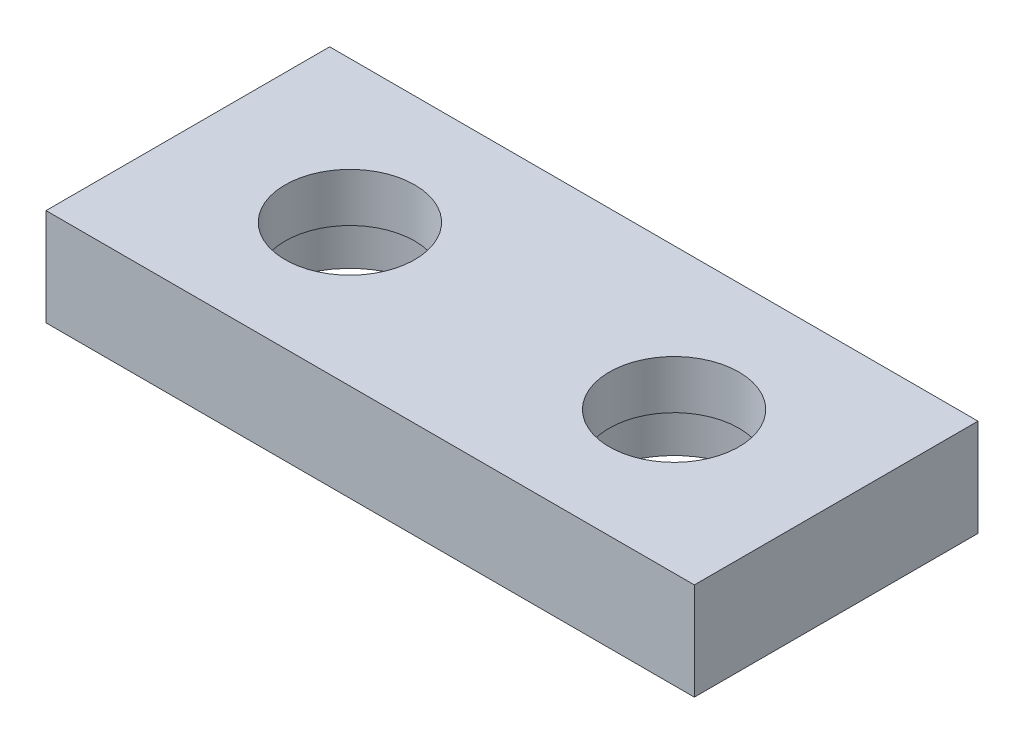
SolidWorks part; units mm, degrees
ref_plane "Front Plane" through (0, 0, 0) normal (0, 0, 1) x (1, 0, 0)
ref_plane "Top Plane" through (0, 0, 0) normal (0, 1, 0) x (1, 0, 0)
ref_plane "Right Plane" through (0, 0, 0) normal (1, 0, 0) x (0, 0, -1)
sketch "Sketch5" plane through (0, 0, 0) normal (0, 1, 0) x (1, 0, 0)
  line L1 (20, -8.75) -> (-20, -8.75)
  line L2 (20, -8.75) -> (20, 8.75)
  line L3 (20, 8.75) -> (-20, 8.75)
  line L4 (-20, -8.75) -> (-20, 8.75)
  line L5 (20, -8.75) -> (-20, 8.75) construction
  line L6 (20, 8.75) -> (-20, -8.75) construction
  point P0 (0, 0)
extrude "Extrude8" add sketch "Sketch5" along normal blind 6
sketch "Sketch7" plane through (0, 0, 0) normal (0, -1, 0) x (1, 0, 0)
  line L0 (0, 0) -> (-20, 0) construction
  line L1 (-20, -8.75) -> (-20, 8.75) construction
  circle A0 centre (-10, 0) radius 5
extrude "Extrude9" cut sketch "Sketch7" against normal blind 3
sketch "Sketch8" plane through (0, 3, 0) normal (0, -1, 0) x (1, 0, 0)
  circle A0 centre (-10, 0) radius 4
extrude "Extrude10" cut sketch "Sketch8" against normal blind 3
mirror "Mirror2" about plane through (0, 0, 0) normal (1, 0, 0) of "Extrude10", "Extrude9"
